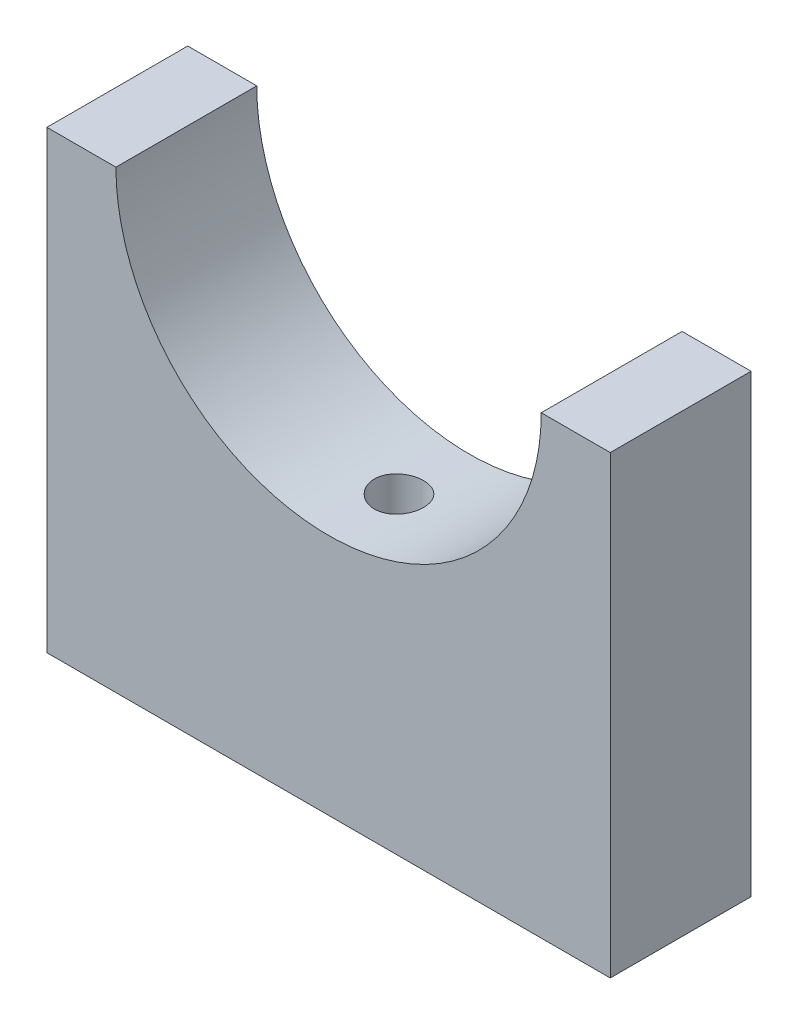
SolidWorks part; units mm, degrees
ref_plane "Front Plane" through (0, 0, 0) normal (0, 0, 1) x (1, 0, 0)
ref_plane "Top Plane" through (0, 0, 0) normal (0, 1, 0) x (1, 0, 0)
ref_plane "Right Plane" through (0, 0, 0) normal (1, 0, 0) x (0, 0, -1)
sketch "Sketch1" plane through (0, 0, 0) normal (0, 0, 1) x (1, 0, 0)
  line L1 (-40, 32.31) -> (40, 32.31)
  line L2 (-40, 32.31) -> (-40, -32.31)
  line L3 (-40, -32.31) -> (40, -32.31)
  line L4 (40, 32.31) -> (40, -32.31)
  line L5 (-40, 32.31) -> (40, -32.31) construction
  line L6 (-40, -32.31) -> (40, 32.31) construction
  point P0 (0, 0)
  dimension "D1" = 64.62
  dimension "D2" = 80
extrude "Boss-Extrude1" add sketch "Sketch1" along normal mid plane 20
sketch "Sketch2" plane through (0, 0, 10) normal (0, 0, 1) x (1, 0, 0)
  line L0 (40, 32.31) -> (-40, 32.31) construction
  line L2 (-30.2, 32.31) -> (30.2, 32.31)
  arc A0 (-30.2, 32.31) -> (30.2, 32.31) centre (0, 32.31) ccw
  dimension "D1" = 30.2
extrude "Cut-Extrude1" cut sketch "Sketch2" against normal up to surface (20 mm away) up to face at (0, 0, -10)
sketch "Sketch3" plane through (0, -32.31, 0) normal (0, -1, 0) x (1, 0, 0)
  point P0 (0, 0)
hole_wizard "M6 Clearance Hole1" positions "Sketch4" profile "Sketch5" hole size "M6" standard "ANSI Metric" end condition through all
sketch "Sketch4" plane through (0, -32.31, 0) normal (0, -1, 0) x (-1, 0, 0)
  point P0 (0, 0)
sketch "Sketch5" plane through (0, -32.31, 0) normal (1, 0, 0) x (0, 0, -1)
  line L0 (0, 0) -> (0, 64.62)
  line L1 (0, 64.62) -> (3.5, 64.62)
  line L2 (3.5, 64.62) -> (3.5, 0)
  line L5 (3.5, 0) -> (0, 0)
  line L11 (0, -6.35) -> (0, 107.95) construction
  dimension "Thru Hole Dia." = 7
  dimension "Thru Hole Depth" = 64.62
